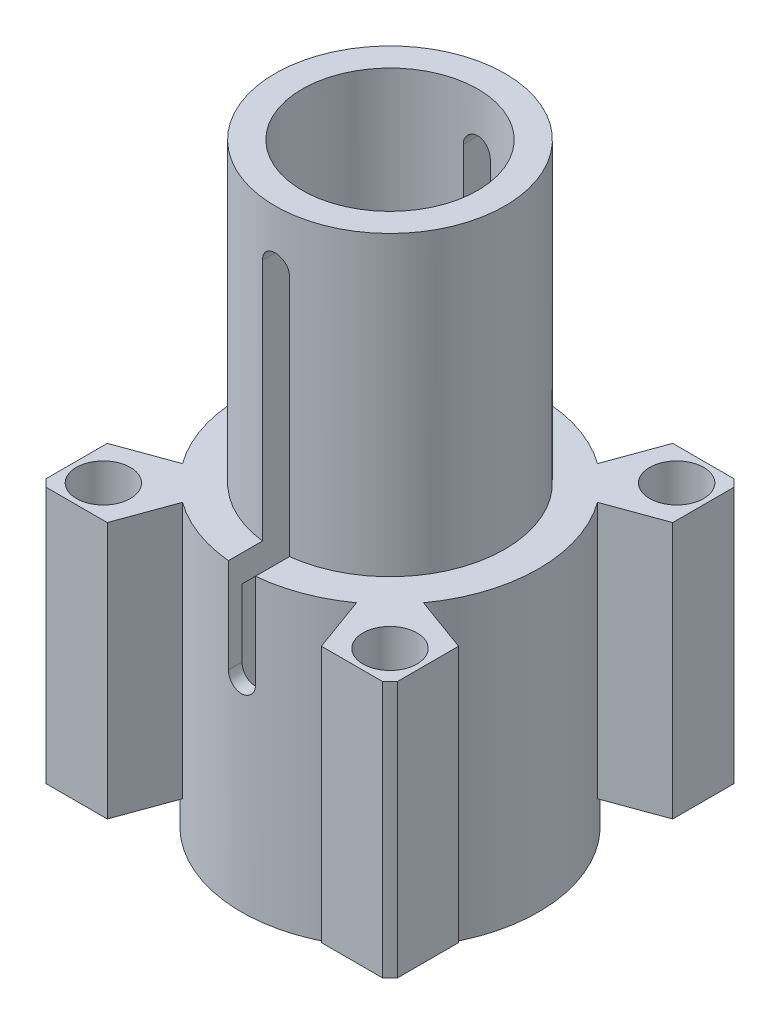
SolidWorks part; units mm, degrees
ref_plane "Plan de face" through (0, 0, 0) normal (0, 0, 1) x (1, 0, 0)
ref_plane "Plan de dessus" through (0, 0, 0) normal (0, 1, 0) x (1, 0, 0)
ref_plane "Plan de droite" through (0, 0, 0) normal (1, 0, 0) x (0, 0, -1)
sketch "Esquisse1" plane through (0, 0, 0) normal (0, 0, 1) x (1, 0, 0)
  line L0 (-6.5, 17) -> (-6.5, 41)
  line L1 (-11, 19) -> (-11, -3)
  line L2 (-11, -3) -> (-10, -3)
  line L3 (-10, -3) -> (-10, 17)
  line L4 (-8.5, 19) -> (-8.5, 41)
  line L5 (-10, 17) -> (-6.5, 17)
  line L6 (-11, 19) -> (-8.5, 19)
  line L7 (-8.5, 41) -> (-6.5, 41)
  line L8 (-11, 19) -> (-10, 19) construction
  line L9 (-10, 41) -> (-6.5, 41) construction
  line L10 (-11, 17) -> (-10, 17) construction
  line L12 (0, 0) -> (0, 14.9808) construction
  line L15 (-10, 17) -> (-6.5, 17) construction
  line L16 (-8.5, 0) -> (-8.5, 14.9808) construction
  line L18 (-6.5, 0) -> (-6.5, 14.9808) construction
revolve "Révolution1" add sketch "Esquisse1" angle 360 about L12
sketch "Esquisse2" plane through (0, 41, 0) normal (0, 1, 0) x (1, 0, 0)
  line L0 (-0.55, -6.4767) -> (-0.55, -9)
  line L3 (-0.55, -9) -> (0.55, -9)
  line L4 (0.55, -6.4767) -> (0.55, -9)
  arc A1 (-0.55, -6.4767) -> (0.55, -6.4767) centre (0, 0) ccw
sketch "Esquisse3" plane through (0, 19, 0) normal (0, 1, 0) x (1, 0, 0)
  line L0 (-12.4499, -13) -> (-7.9241, -13)
  line L1 (12.4499, 13) -> (7.9241, 13)
  line L2 (13, 12.4499) -> (13, 7.9241)
  line L3 (-13, -12.4499) -> (-13, -7.9241)
  line L4 (0, 0) -> (0, 4.2793) construction
  line L5 (0, 0) -> (-3.606, 0) construction
  line L6 (8.9187, 6.4387) -> (13, 7.9241)
  line L7 (13, -7.9241) -> (13, -12.4499)
  line L8 (6.4387, -8.9187) -> (7.9241, -13)
  line L9 (-6.4387, -8.9187) -> (-7.9241, -13)
  line L10 (8.9187, -6.4387) -> (13, -7.9241)
  line L11 (-8.9187, -6.4387) -> (-13, -7.9241)
  line L12 (-8.9187, 6.4387) -> (-13, 7.9241)
  line L13 (-6.4387, 8.9187) -> (-7.9241, 13)
  line L14 (6.4387, 8.9187) -> (7.9241, 13)
  line L15 (-7.9241, 13) -> (-12.4499, 13)
  line L16 (-13, 7.9241) -> (-13, 12.4499)
  line L17 (7.9241, -13) -> (12.4499, -13)
  circle A0 centre (10.6066, 10.6066) radius 2
  arc A1 (8.9187, -6.4387) -> (8.9187, 6.4387) centre (0, 0) ccw
  circle A2 centre (-10.6066, -10.6066) radius 2
  circle A3 centre (-10.6066, 10.6066) radius 2
  circle A4 centre (10.6066, -10.6066) radius 2
  arc A5 (-13, -12.4499) -> (-12.4499, -13) centre (0, 0) ccw
  arc A6 (-12.4499, 13) -> (-13, 12.4499) centre (0, 0) ccw
  arc A7 (13, 12.4499) -> (12.4499, 13) centre (0, 0) ccw
  arc A8 (12.4499, -13) -> (13, -12.4499) centre (0, 0) ccw
  arc A9 (6.4387, 8.9187) -> (-6.4387, 8.9187) centre (0, 0) ccw
  arc A10 (-8.9187, 6.4387) -> (-8.9187, -6.4387) centre (0, 0) ccw
  circle A12 centre (0, 0) radius 10
  arc A13 (-6.4387, -8.9187) -> (6.4387, -8.9187) centre (0, 0) ccw
extrude "Extrusion2" add sketch "Esquisse3" against normal blind 19
sketch "Esquisse4" plane through (0, 0, 13) normal (0, 0, 1) x (1, 0, 0)
  line L0 (0, 0) -> (0, 46.1813) construction
  line L3 (-1, 37) -> (-1, 12)
  line L4 (1, 12) -> (1, 37)
  arc A0 (-1, 12) -> (1, 12) centre (0, 12) ccw
  arc A1 (1, 37) -> (-1, 37) centre (0, 37) ccw
extrude "Extrusion4" cut sketch "Esquisse4" against normal through all
